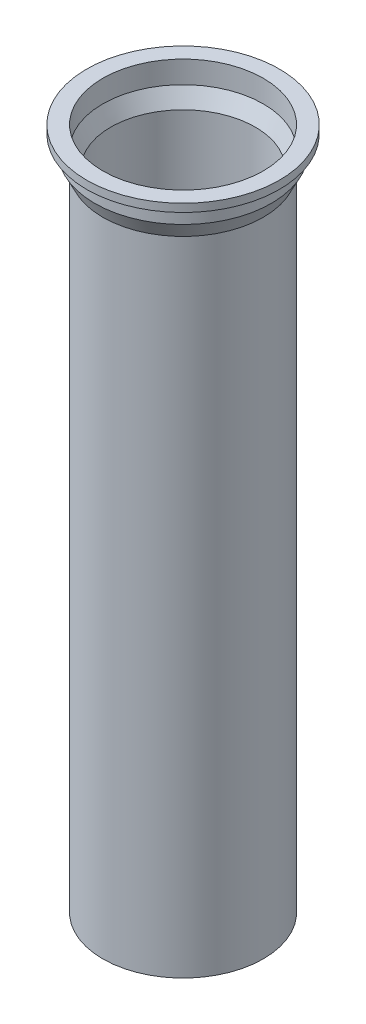
SolidWorks part; units mm, degrees
ref_plane "Alzado" through (0, 0, 0) normal (0, 0, 1) x (1, 0, 0)
ref_plane "Planta" through (0, 0, 0) normal (0, 1, 0) x (1, 0, 0)
ref_plane "Vista lateral" through (0, 0, 0) normal (1, 0, 0) x (0, 0, -1)
sketch "Croquis5" plane through (0, 0, 0) normal (0, 0, 1) x (1, 0, 0)
  line L0 (0, 0) -> (0, -55.2978) construction
  line L1 (0, 0) -> (-60, 0) construction
  line L2 (-60, 0) -> (-60, -5)
  line L3 (-60, -5) -> (-55, -5)
  line L4 (-55, -5) -> (-55, -15)
  line L5 (-55, -15) -> (-50, -25)
  line L6 (-50, -25) -> (-50, -425)
  line L7 (-50, -425) -> (-45, -425)
  line L8 (-45, -425) -> (-45, -23.8197)
  line L9 (-45, -23.8197) -> (-50, -13.8197)
  line L10 (-50, -13.8197) -> (-50, 0)
  line L11 (-50, 0) -> (-60, 0)
  point P3 (0, 0)
  point P14 (0, 0)
  point P15 (-45, -29.3671)
  point P16 (0, 0)
  dimension "D1" = 60
  dimension "D2" = 50
  dimension "D3" = 5
  dimension "D4" = 55
  dimension "D5" = 45
  dimension "D6" = 50
  dimension "D7" = 400
  dimension "D8" = 5
  dimension "D9" = 10
  dimension "D10" = 10
revolve "Revolución1" add sketch "Croquis5" angle 360 about L0
